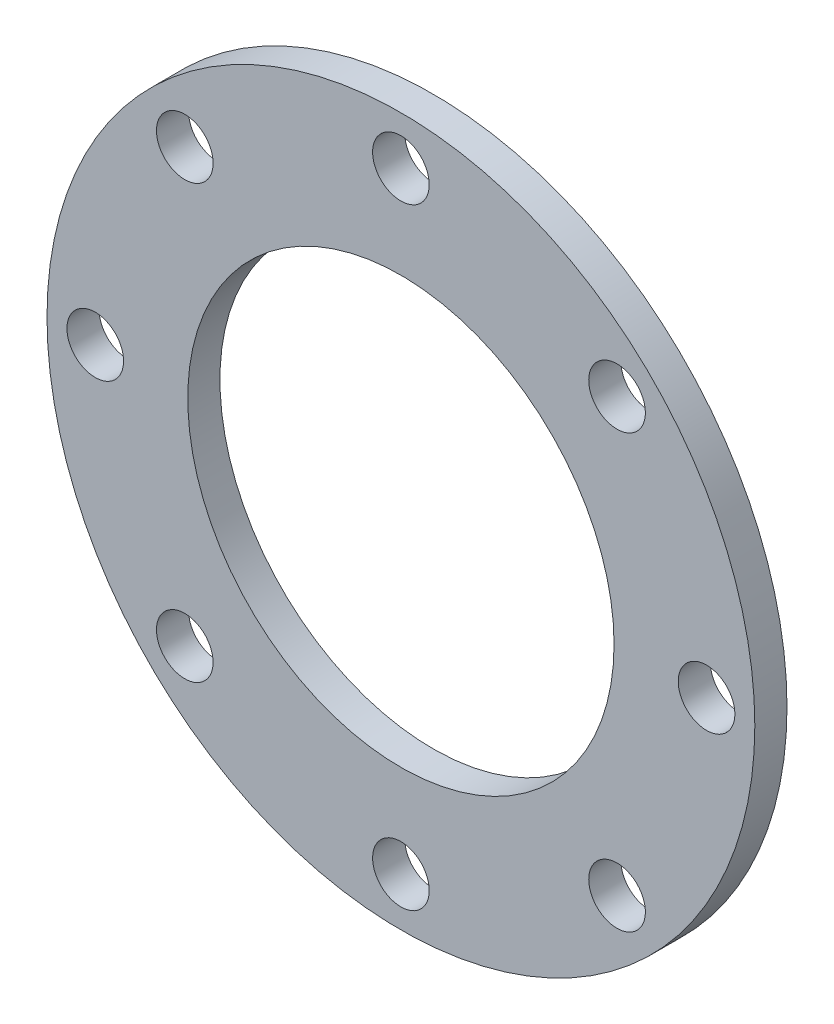
SolidWorks part; units mm, degrees
material "Ductile Iron"
ref_plane "Front Plane" through (0, 0, 0) normal (0, 0, 1) x (1, 0, 0)
ref_plane "Top Plane" through (0, 0, 0) normal (0, 1, 0) x (1, 0, 0)
ref_plane "Right Plane" through (0, 0, 0) normal (1, 0, 0) x (0, 0, -1)
sketch "Sketch1" plane through (0, 0, 0) normal (0, 0, 1) x (1, 0, 0)
  circle A0 centre (0, 0) radius 139.7
  circle A1 centre (0, 0) radius 120.65 construction
  circle A2 centre (0, 0) radius 84.1375
  circle A3 centre (0, 120.65) radius 11.176 construction
  circle A4 centre (85.3124, 85.3124) radius 11.176 construction
  circle A5 centre (120.65, 0) radius 11.176 construction
  circle A6 centre (85.3124, -85.3124) radius 11.176 construction
  circle A7 centre (0, -120.65) radius 11.176 construction
  circle A8 centre (-85.3124, -85.3124) radius 11.176 construction
  circle A9 centre (-120.65, 0) radius 11.176 construction
  circle A10 centre (-85.3124, 85.3124) radius 11.176 construction
  point P8 (0, 120.65)
  point P9 (0, 0)
  point P23 (0, 0)
  point P24 (0, -120.65)
  dimension "D1" = 279.4
  dimension "D2" = 241.3
  dimension "D3" = 168.275
  dimension "D4" = 22.352
  dimension "D5" = 8
extrude "Boss-Extrude1" add sketch "Sketch1" along normal blind 12.7
hole_wizard "7/8 (0.88) Diameter Hole1" positions "3DSketch1" profile "Sketch2" hole size "7/8" standard "ANSI Inch" end condition through all
sketch3d "3DSketch1"
  point P0 (120.65, 0, 0)
  point P3 (120.65, 0, 12.7)
  point P7 (0, 0, 0)
sketch "Sketch2" plane through (120.65, 0, 12.7) normal (1, 0, 0) x (0, -1, 0)
  line L0 (0, 0) -> (0, 12.7)
  line L1 (0, 12.7) -> (11.176, 12.7)
  line L2 (11.176, 12.7) -> (11.176, 0)
  line L5 (11.176, 0) -> (0, 0)
  line L11 (0, -6.35) -> (0, 107.95) construction
  dimension "Thru Hole Dia." = 22.352
  dimension "Thru Hole Depth" = 12.7
pattern_circular "CirPattern1" count 8 over 360 about axis through (0, 0, 0) along (0, 0, 1) of "7/8 (0.88) Diameter Hole1"
equation "\"ID\"= 6.62500000in"
equation "\"BC\"= 9.5in"
equation "\"OD\"= 11in"
equation "\"HD\"= 0.88in"
equation "\"T\"= 0.5in"
equation "\"D1@Sketch1\"=\"OD\""
equation "\"D2@Sketch1\"=\"BC\""
equation "\"D3@Sketch1\"=\"ID\""
equation "\"D4@Sketch1\"=\"HD\""
equation "\"D1@Boss-Extrude1\"=\"T\""
